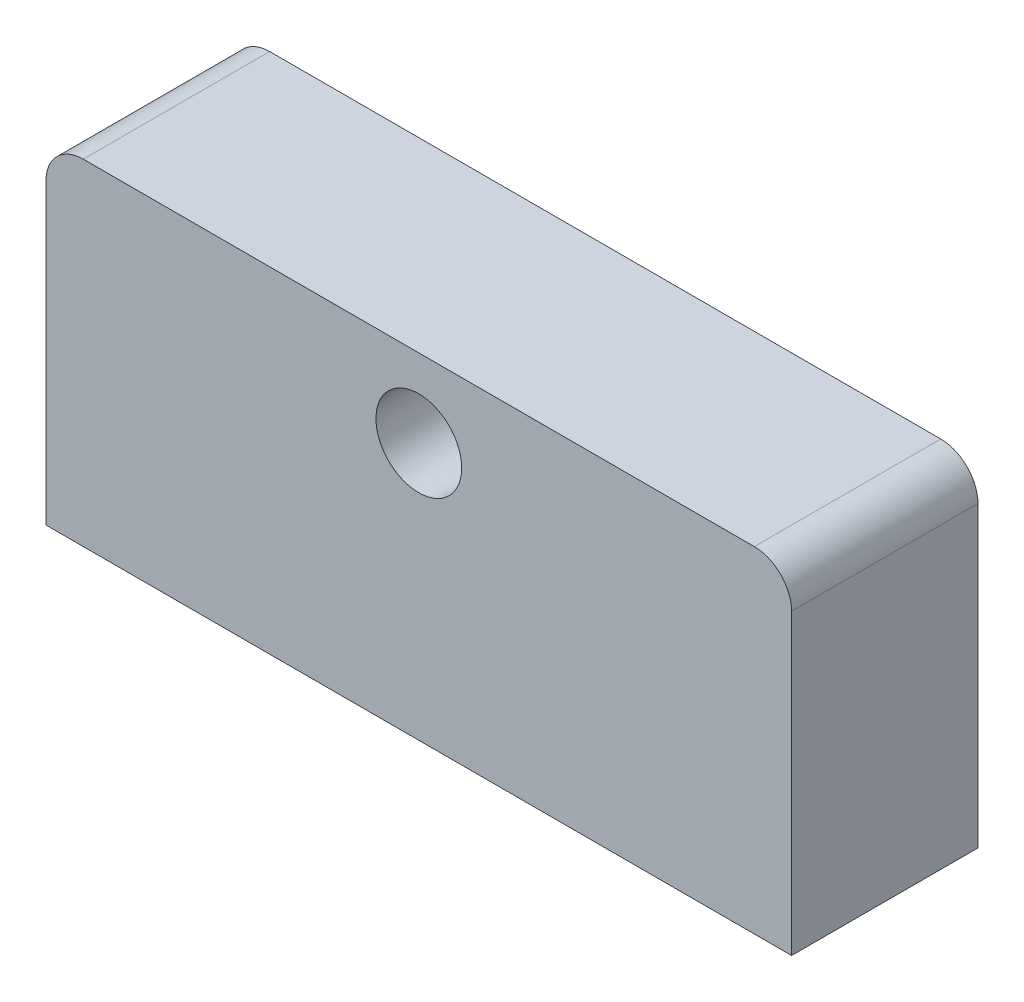
SolidWorks part; units mm, degrees
ref_plane "Front Plane" through (0, 0, 0) normal (0, 0, 1) x (1, 0, 0)
ref_plane "Top Plane" through (0, 0, 0) normal (0, 1, 0) x (1, 0, 0)
ref_plane "Right Plane" through (0, 0, 0) normal (1, 0, 0) x (0, 0, -1)
sketch "Sketch1" plane through (0, 0, 0) normal (0, 0, 1) x (1, 0, 0)
  line L0 (0, -45) -> (0, -5) construction
  line L1 (100, -45) -> (-100, -45)
  line L2 (100, -45) -> (100, 45)
  line L3 (100, 45) -> (-100, 45)
  line L4 (-100, -45) -> (-100, 45)
  line L5 (100, -45) -> (-100, 45) construction
  line L6 (100, 45) -> (-100, -45) construction
  circle A1 centre (0, 24) radius 11.5
  circle A2 centre (-15.5, 39.5) radius 1.75
  circle A3 centre (-15.5, 8.5) radius 1.75
  circle A4 centre (15.5, 8.5) radius 1.75
  circle A5 centre (15.5, 39.5) radius 1.75
  point P0 (0, 0)
  dimension "D2" = 23
  dimension "D4" = 21
  dimension "D5" = 40
  dimension "D7" = 15.5
  dimension "D8" = 15.5
  dimension "D9" = 15.5
  dimension "D10" = 15.5
  dimension "D11" = 15.5
  dimension "D12" = 15.5
  dimension "D13" = 15.5
  dimension "D14" = 15.5
  dimension "D15" = 3.5
  dimension "D1" = 200
  dimension "D3" = 90
  dimension "D6" = 29
extrude "Boss-Extrude1" add sketch "Sketch1" along normal mid plane 50 contours A1 | L2 L1 L4 L3
sketch "Sketch2" plane through (0, 0, -25) normal (0, 0, -1) x (-1, 0, 0)
  circle A0 centre (-15.5, 8.5) radius 1.75 construction
  circle A1 centre (-15.5, 8.5) radius 1.75
  circle A2 centre (15.5, 8.5) radius 1.75 construction
  circle A3 centre (15.5, 8.5) radius 1.75
  circle A4 centre (15.5, 39.5) radius 1.75 construction
  circle A5 centre (15.5, 39.5) radius 1.75
  circle A6 centre (-15.5, 39.5) radius 1.75 construction
  circle A7 centre (-15.5, 39.5) radius 1.75
extrude "Cut-Extrude1" cut sketch "Sketch2" against normal blind 10
sketch "Sketch3" plane through (0, -45, 0) normal (0, -1, 0) x (1, 0, 0)
  line L0 (100, 0) -> (-100, 0) construction
  line L1 (100, 0) -> (-100, 0) construction
  line L2 (-100, 25) -> (-100, -25) construction
  line L3 (100, 25) -> (100, -25) construction
  circle A0 centre (-50, 0) radius 5
  circle A1 centre (50, 0) radius 5
  dimension "D1" = 10
  dimension "D3" = 10
  dimension "D4" = 50
  dimension "D2" = 50
extrude "Cut-Extrude2" cut sketch "Sketch3" against normal blind 15
fillet "Fillet1" radius 10 2 edges at (-100, 45, 0) (100, 45, 0)
